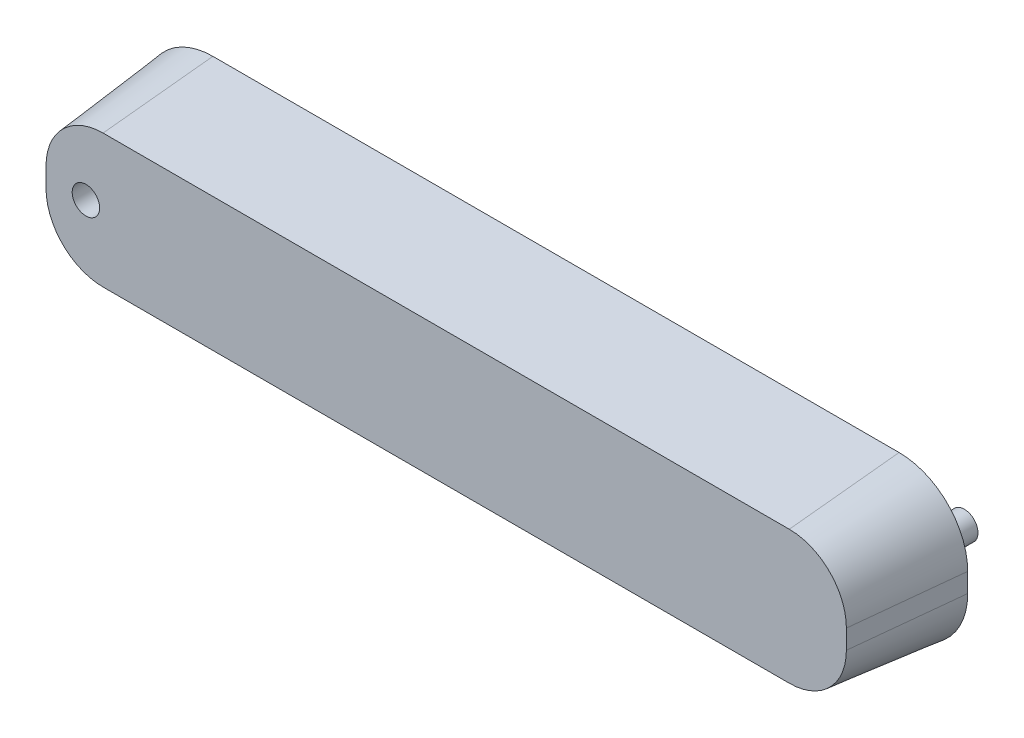
SolidWorks part; units mm, degrees
ref_plane "Front Plane" through (0, 0, 0) normal (0, 0, 1) x (1, 0, 0)
ref_plane "Top Plane" through (0, 0, 0) normal (0, 1, 0) x (1, 0, 0)
ref_plane "Right Plane" through (0, 0, 0) normal (1, 0, 0) x (0, 0, -1)
sketch "Sketch1" plane through (0, 0, 0) normal (0, 1, 0) x (1, 0, 0)
  line L1 (-250, 57) -> (250, 57)
  line L2 (-300, 7) -> (-300, -7)
  line L3 (-250, -57) -> (250, -57)
  line L4 (300, 7) -> (300, -7)
  line L5 (-300, 57) -> (300, -57) construction
  line L6 (-300, -57) -> (300, 57) construction
  arc A0 (300, 7) -> (250, 57) centre (250, 7) ccw
  arc A1 (300, -7) -> (250, -57) centre (250, -7) cw
  arc A2 (-250, 57) -> (-300, 7) centre (-250, 7) ccw
  arc A3 (-300, -7) -> (-250, -57) centre (-250, -7) ccw
  point P0 (0, 0)
  dimension "D3" = 50
  dimension "D4" = 50
  dimension "D5" = 50
  dimension "D6" = 50
  dimension "D1" = 600
  dimension "D2" = 114
extrude "Boss-Extrude1" add sketch "Sketch1" along normal blind 80 draft 6 contours L1 A0 L4 A1 L3 A3 L2 A2
sketch "Sketch2" plane through (0, 0, 0) normal (0, -1, 0) x (1, 0, 0)
  line L0 (0, 0) -> (262.5, 0)
  circle A0 centre (262.5, 0) radius 10
  dimension "D1" = 262.5
  dimension "D2" = 20
extrude "Boss-Extrude2" add sketch "Sketch2" along normal blind 35 contours A0
sketch "Sketch3" plane through (0, 80, 0) normal (0, 1, 0) x (1, 0, 0)
  line L0 (0, 0) -> (-262.5, 0)
  circle A0 centre (-262.5, 0) radius 10
  dimension "D2" = 20
  dimension "D1" = 262.5
extrude "Cut-Extrude1" cut sketch "Sketch3" against normal blind 30 contours A0
sketch "Sketch4" plane through (0, 0, 0) normal (0, 1, 0) x (1, 0, 0)
  point P0 (-262.5, 0)
move or copy body "Body-Move/Copy1" bodies to move or copy 103 copy no translate (262.5, 0, 0)
move or copy body "Body-Move/Copy2" bodies to move or copy 104 copy no rotation origin (0, 0, 0) rotation axis (1, 0, 0) rotation angle 90
